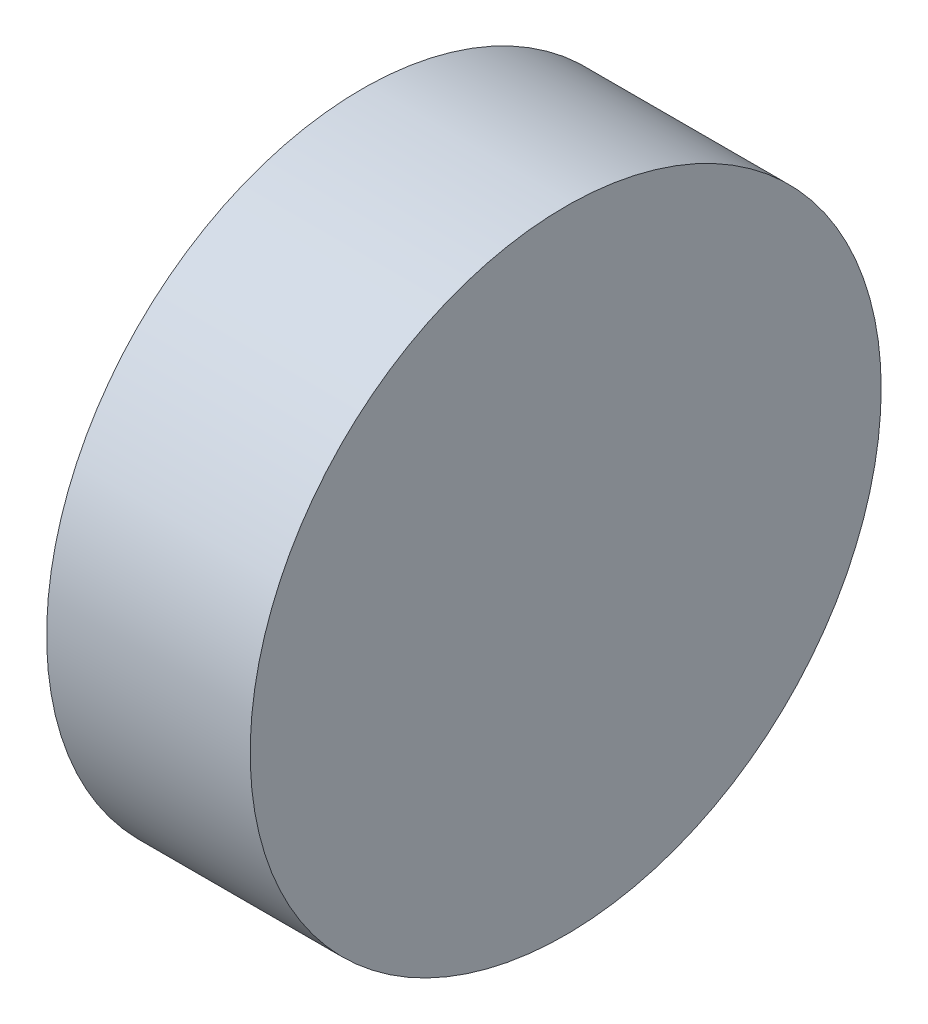
SolidWorks part; units mm, degrees
ref_plane "Front Plane" through (0, 0, 0) normal (0, 0, 1) x (1, 0, 0)
ref_plane "Top Plane" through (0, 0, 0) normal (0, 1, 0) x (1, 0, 0)
ref_plane "Right Plane" through (0, 0, 0) normal (1, 0, 0) x (0, 0, -1)
sketch "Sketch1" plane through (0, 0, 0) normal (1, 0, 0) x (0, 0, -1)
  circle A0 centre (0, 0) radius 3.937
extrude "Boss-Extrude1" add sketch "Sketch1" along normal blind 2.54 contours A0
